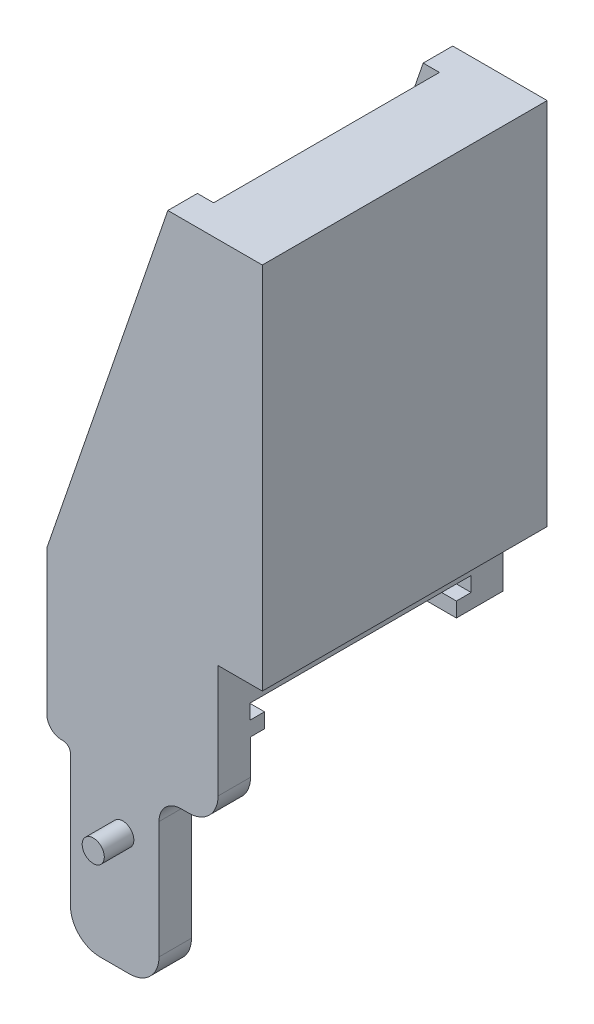
SolidWorks part; units mm, degrees
ref_plane "Alzado" through (0, 0, 0) normal (0, 0, 1) x (1, 0, 0)
ref_plane "Planta" through (0, 0, 0) normal (0, 1, 0) x (1, 0, 0)
ref_plane "Vista lateral" through (0, 0, 0) normal (1, 0, 0) x (0, 0, -1)
sketch "Croquis1" plane through (0, 0, 0) normal (0, 0, 1) x (1, 0, 0)
  line L0 (5.8, 23.05) -> (2.4, 23.05)
  line L2 (2.4, 23.05) -> (-5.8, -0.85)
  line L9 (1.8, -13.107) -> (1.8, -21.05)
  line L10 (-0.2, -23.05) -> (-2.2, -23.05)
  line L11 (-4.2, -21.05) -> (-4.2, -12.1093)
  line L12 (-4.7023, -11.6093) -> (-4.7953, -11.6097)
  line L13 (-5.8, -10.6097) -> (-5.8, -0.85)
  line L14 (3.3, -11.607) -> (3.8, -11.607)
  line L15 (5.8, -9.607) -> (5.8, 23.05)
  arc A0 (3.8, -11.607) -> (5.8, -9.607) centre (3.8, -9.607) ccw
  arc A1 (1.8, -13.107) -> (3.3, -11.607) centre (3.3, -13.107) cw
  arc A2 (1.8, -21.05) -> (-0.2, -23.05) centre (-0.2, -21.05) cw
  arc A3 (-2.2, -23.05) -> (-4.2, -21.05) centre (-2.2, -21.05) cw
  arc A4 (-4.7953, -11.6097) -> (-5.8, -10.6097) centre (-4.8, -10.6097) cw
  arc A5 (-4.2, -12.1093) -> (-4.7023, -11.6093) centre (-4.7, -12.1093) ccw
  point P0 (0, 0)
  dimension "D1" = 2
  dimension "D2" = 1.5
  dimension "D3" = 1
  dimension "D4" = 1.8
  dimension "D5" = 2.4
  dimension "D6" = 4.7023
  dimension "D7" = 4.7953
  dimension "D8" = 23.05
  dimension "D9" = 0.85
  dimension "D10" = 10.6097
  dimension "D11" = 11.607
  dimension "D12" = 23.05
extrude "Saliente-Extruir1" add sketch "Croquis1" along normal blind 19.3
sketch "Croquis2" plane through (-5.8, 0, 0) normal (-1, 0, 0) x (0, 0, 1)
  line L0 (0, -0.85) -> (0, -10.6097) construction
  line L1 (19.3, 23.05) -> (0, 23.05) construction
  line L2 (19.3, -10.6097) -> (0, -10.6097) construction
  line L3 (17.3, -3.25) -> (17.3, 23.05)
  line L4 (2, -3.25) -> (17.3, -3.25)
  line L5 (17.3, 23.05) -> (2, 23.05)
  line L6 (2, 23.05) -> (2, -3.25)
  dimension "D1" = 2
  dimension "D2" = 17.3
  dimension "D3" = 7.3597
extrude "Cortar-Extruir1" cut sketch "Croquis2" against normal blind 9.3 contours L3 L5 L6 L4
sketch "Croquis4" plane through (-5.8, 0, 0) normal (-1, 0, 0) x (0, 0, 1)
  line L0 (2.15, -5.2399) -> (2.15, -6.2399)
  line L1 (17.15, -5.2399) -> (2.15, -5.2399)
  line L2 (2.15, -6.2399) -> (3.15, -6.2399)
  line L3 (3.15, -6.2399) -> (3.15, -7.2399)
  line L4 (3.15, -7.2399) -> (-0.05, -7.2399)
  line L5 (-0.05, -7.2399) -> (-0.05, -23.2399)
  line L6 (-0.05, -23.2399) -> (17.1, -23.2399)
  line L7 (17.15, -5.2399) -> (17.15, -6.2399)
  line L8 (17.15, -6.2399) -> (16.15, -6.2399)
  line L9 (16.15, -6.2399) -> (16.15, -7.2399)
  line L11 (16.15, -7.2399) -> (17.1, -7.2399)
  line L12 (17.1, -7.2399) -> (17.1, -23.2399)
  line L14 (0, -0.85) -> (0, -10.6097) construction
  line L15 (2, -0.85) -> (0, -0.85) construction
  dimension "D1" = 2.15
  dimension "D2" = 3.15
  dimension "D3" = 16.15
  dimension "D4" = 17.1
  dimension "D5" = 0.05
  dimension "D6" = 4.3899
  dimension "D7" = 22.3899
extrude "Cortar-Extruir2" cut sketch "Croquis4" against normal blind 12.3
sketch "Croquis6" plane through (0, 0, 19.3) normal (0, 0, 1) x (1, 0, 0)
  circle A0 centre (-0.6552, -15.0462) radius 0.75
extrude "Saliente-Extruir2" add sketch "Croquis6" along normal blind 2
sketch "Croquis7" plane through (5.8, 0, 0) normal (1, 0, 0) x (0, 0, -1)
  line L0 (0, -7.2399) -> (0, 23.05) construction
  line L1 (-19.3, 23.05) -> (0, 23.05)
  line L2 (-19.3, 23.05) -> (-19.3, -1.95)
  line L3 (-19.3, -1.95) -> (0, -1.95)
  line L4 (0, 23.05) -> (0, -1.95)
  dimension "D1" = 25
extrude "Saliente-Extruir3" add sketch "Croquis7" along normal blind 3
